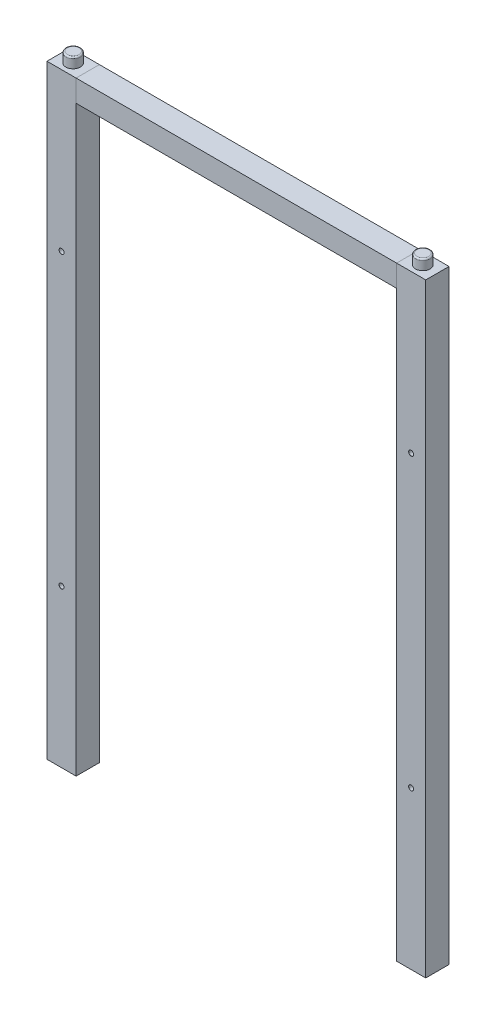
SolidWorks part; units mm, degrees
other "Top Bar"
other "Right Bar"
other "Left Bar"
ref_plane "Front Plane" through (0, 0, 0) normal (0, 0, 1) x (1, 0, 0)
ref_plane "Top Plane" through (0, 0, 0) normal (0, 1, 0) x (1, 0, 0)
ref_plane "Right Plane" through (0, 0, 0) normal (1, 0, 0) x (0, 0, -1)
sketch "Sketch1" plane through (0, 0, 0) normal (1, 0, 0) x (0, 0, -1)
  line L0 (0, 197.2019) -> (0, -217.7981)
  line L1 (0, -217.7981) -> (16, -217.7981)
  line L2 (16, -217.7981) -> (16, 197.2019)
  line L3 (16, 197.2019) -> (0, 197.2019)
  dimension "D1" = 415
  dimension "D2" = 16
ref_plane "Plane1" through (110, 0, 0) normal (-1, 0, 0) x (0, 0, 1)
extrude "Boss-Extrude1" add sketch "Sketch1" against normal blind 20
sketch "Sketch5" plane through (0, 197.2019, 0) normal (0, 1, 0) x (1, 0, 0)
  line L2 (-20, 16) -> (-20, 0) construction
  line L3 (-20, 16) -> (0, 16) construction
  circle A0 centre (-10, 8) radius 5
  dimension "D1" = 10
  dimension "D2" = 10
  dimension "D3" = 8
extrude "Boss-Extrude2" add sketch "Sketch5" along normal blind 7
fillet "Fillet1" radius 1 1 edges at (-10, 204.2019, -3)
sketch "Sketch6" plane through (0, 0, 0) normal (0, 0, 1) x (1, 0, 0)
  line L0 (-20, -217.7981) -> (0, -217.7981) construction
  line L1 (-20, 197.2019) -> (-20, -217.7981) construction
  point P0 (-10, 89.2019)
  point P1 (-10, -109.7981)
  dimension "D1" = 199
  dimension "D2" = 108
  dimension "D3" = 10
hole_wizard "M3 Clearance Hole1" positions "3DSketch1" profile "Sketch7" hole size "M3" standard "ANSI Metric" end condition through all
sketch3d "3DSketch1"
  point P0 (-10, 89.2019, 0)
  point P3 (-10, -109.7981, 0)
sketch "Sketch7" plane through (-10, 89.2019, 0) normal (1, 0, 0) x (0, -1, 0)
  line L0 (0, 0) -> (0, 16)
  line L1 (0, 16) -> (1.7, 16)
  line L2 (1.7, 16) -> (1.7, 0.025)
  line L3 (1.7, 0.025) -> (1.725, 0)
  line L5 (1.725, 0) -> (0, 0)
  line L6 (-1.7, 0.025) -> (-1.725, 0) construction
  line L11 (0, -6.35) -> (0, 107.95) construction
  dimension "Thru Hole Dia." = 3.4
  dimension "Thru Hole Depth" = 16
  dimension "Near C'Sink Dia." = 3.45
  dimension "Near C'Sink Angle" = 90
sketch "Sketch8" plane through (0, -217.7981, 0) normal (0, -1, 0) x (1, 0, 0)
  line L0 (-20, -16) -> (0, -16) construction
  line L1 (-17.5, -0.5) -> (-2.5, -0.5)
  line L2 (-17.5, -0.5) -> (-17.5, -15.5)
  line L3 (-17.5, -15.5) -> (-2.5, -15.5)
  line L4 (-2.5, -0.5) -> (-2.5, -15.5)
  line L5 (-20, 0) -> (-20, -16) construction
  dimension "D1" = 15
  dimension "D2" = 15
  dimension "D3" = 0.5
  dimension "D4" = 2.5
extrude "Cut-Extrude1" cut sketch "Sketch8" against normal blind 7
mirror "Mirror7" about plane through (110, 0, 0) normal (-1, 0, 0) of bodies 104
sketch "Sketch14" plane through (0, 0, 0) normal (0, 0, 1) x (1, 0, 0)
  line L0 (0, 197.2019) -> (220, 197.2019)
  line L1 (220, 197.2019) -> (220, 182.2019)
  line L2 (220, 197.2019) -> (220, -217.7981) construction
  line L3 (220, 182.2019) -> (0, 182.2019)
  line L4 (0, 182.2019) -> (0, 197.2019)
  dimension "D1" = 15
extrude "Boss-Extrude3" add sketch "Sketch14" against normal blind 16 separate body
